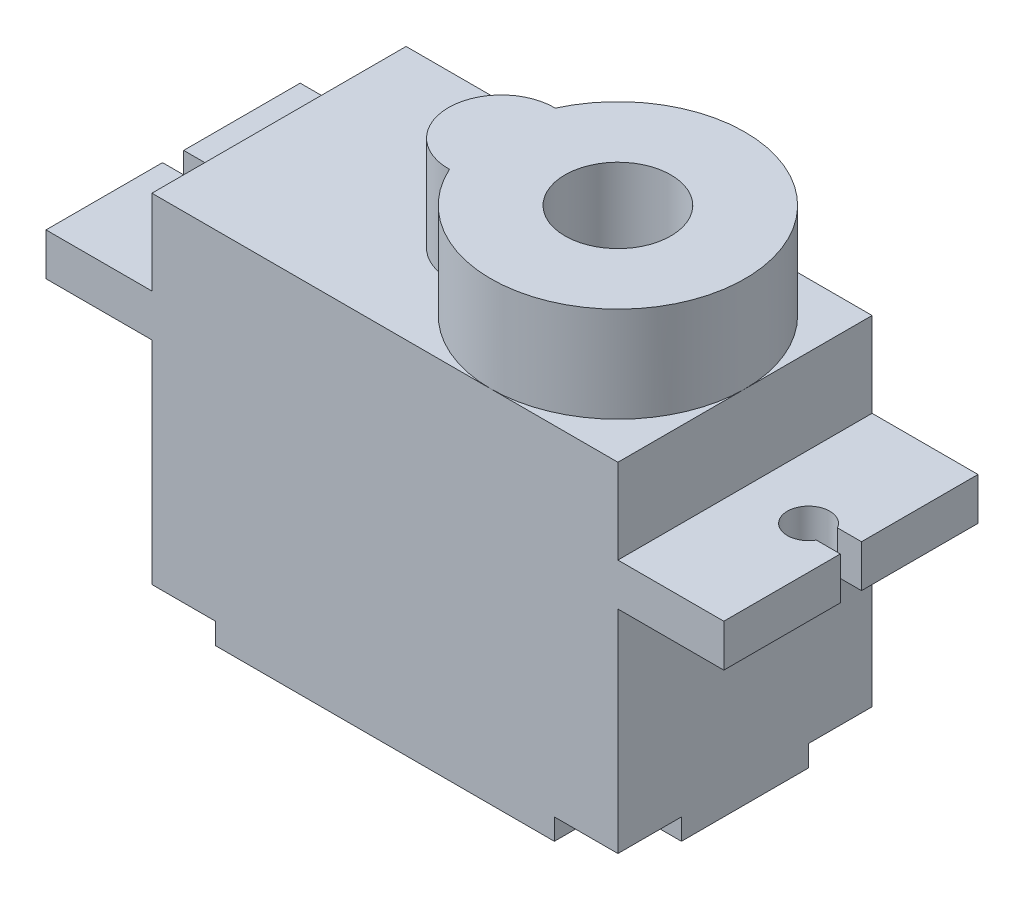
SolidWorks part; units mm, degrees
material "Plástico personalizado"
ref_plane "Alzado" through (0, 0, 0) normal (0, 0, 1) x (1, 0, 0)
ref_plane "Planta" through (0, 0, 0) normal (0, 1, 0) x (1, 0, 0)
ref_plane "Vista lateral" through (0, 0, 0) normal (1, 0, 0) x (0, 0, -1)
sketch "Croquis1" plane through (0, 0, 0) normal (0, 1, 0) x (1, 0, 0)
  line L1 (11, -6) -> (-11, -6)
  line L2 (11, -6) -> (11, 6)
  line L3 (11, 6) -> (-11, 6)
  line L4 (-11, -6) -> (-11, 6)
  line L5 (11, -6) -> (-11, 6) construction
  line L6 (11, 6) -> (-11, -6) construction
  point P0 (0, 0)
  dimension "D1" = 22
  dimension "D2" = 12
extrude "Saliente-Extruir1" add sketch "Croquis1" along normal blind 11
sketch "Croquis3" plane through (0, 11, 0) normal (0, 1, 0) x (1, 0, 0)
  line L0 (-11, 6) -> (-11, -6) construction
  line L1 (-6, 6) -> (-16, 6)
  line L2 (-6, 6) -> (-6, -6)
  line L3 (-6, -6) -> (-16, -6)
  line L4 (-16, 6) -> (-16, -6)
  line L5 (-6, 6) -> (-16, -6) construction
  line L6 (-6, -6) -> (-16, 6) construction
  line L7 (11, -6) -> (11, 6) construction
  line L8 (6, -6) -> (16, -6)
  line L9 (6, -6) -> (6, 6)
  line L10 (6, 6) -> (16, 6)
  line L11 (16, -6) -> (16, 6)
  line L12 (6, -6) -> (16, 6) construction
  line L13 (6, 6) -> (16, -6) construction
  point P0 (-11, 0)
  point P7 (11, 0)
  dimension "D1" = 10
  dimension "D2" = 10
extrude "Saliente-Extruir2" add sketch "Croquis3" along normal blind 2
sketch "Croquis4" plane through (0, 11, 0) normal (0, 1, 0) x (1, 0, 0)
  line L1 (6, -6) -> (-6, -6)
  line L2 (6, -6) -> (6, 6)
  line L3 (6, 6) -> (-6, 6)
  line L4 (-6, -6) -> (-6, 6)
  line L5 (6, -6) -> (-6, 6) construction
  line L6 (6, 6) -> (-6, -6) construction
  point P0 (0, 0)
extrude "Saliente-Extruir3" add sketch "Croquis4" along normal blind 6
sketch "Croquis5" plane through (0, 13, 0) normal (0, 1, 0) x (1, 0, 0)
  line L0 (-16, 0) -> (-16, 0.5)
  line L1 (-16, 6) -> (-16, -6) construction
  line L2 (-16, 0) -> (-16, -0.5)
  line L3 (-16, 0) -> (-15, 0)
  line L4 (-16, 0.5) -> (-15, 0.5)
  line L5 (-16, -0.5) -> (-15.9117, -0.5)
  line L7 (-15.9117, -0.5) -> (-15, -0.5)
  line L9 (-15, 0.5) -> (-14.866, 0.5)
  line L10 (-15, -0.5) -> (-14.866, -0.5)
  arc A0 (-14.866, -0.5) -> (-14.866, 0.5) centre (-14, 0) ccw
  dimension "D1" = 0.5
  dimension "D2" = 0.5
  dimension "D3" = 1
  dimension "D4" = 1
extrude "Cortar-Extruir1" cut sketch "Croquis5" against normal blind 2
sketch "Croquis6" plane through (0, 13, 0) normal (0, 1, 0) x (1, 0, 0)
  line L0 (6, -6) -> (16, -6) construction
  line L1 (-6, 6) -> (-11, 6)
  line L2 (-6, 6) -> (-6, -6)
  line L3 (-6, -6) -> (-11, -6)
  line L4 (-11, 6) -> (-11, -6)
  line L5 (6, 6) -> (11, 6)
  line L6 (6, 6) -> (6, -6)
  line L7 (6, -6) -> (11, -6)
  line L8 (11, 6) -> (11, -6)
extrude "Saliente-Extruir4" add sketch "Croquis6" along normal blind 4
sketch "Croquis7" plane through (0, 13, 0) normal (0, 1, 0) x (1, 0, 0)
  line L1 (16, -6) -> (16, 6) construction
  line L2 (16, 0) -> (16, 0.5)
  line L3 (16, 0) -> (16, -0.5)
  line L5 (16, 0.5) -> (14.907, 0.5)
  line L6 (16, -0.5) -> (15, -0.5)
  line L7 (15, -0.5) -> (14.866, -0.5)
  line L8 (14.907, 0.5) -> (14.866, 0.5)
  arc A0 (14.866, 0.5) -> (14.866, -0.5) centre (14, 0) ccw
  dimension "D2" = 0.5
  dimension "D3" = 0.5
extrude "Cortar-Extruir2" cut sketch "Croquis7" against normal blind 4
sketch "Croquis8" plane through (0, 17, 0) normal (0, 1, 0) x (1, 0, 0)
  circle A0 centre (5, 0) radius 6
extrude "Saliente-Extruir5" add sketch "Croquis8" along normal blind 4.5
sketch "Croquis9" plane through (0, 17, 0) normal (0, 1, 0) x (1, 0, 0)
  line L0 (11, 0) -> (-0.5, 0)
  line L1 (11, -6) -> (11, 6) construction
  circle A0 centre (-0.5, 0) radius 2.5
  arc M2 (5, -6) -> (5, 6) centre (5, 0) cw
  dimension "D2" = 5
  dimension "D1" = 11.5
extrude "Saliente-Extruir6" add sketch "Croquis9" along normal up to surface (4.5 mm away) contours A0 M2 up to face at (5, 21.5, 6)
sketch "Croquis10" plane through (0, 0, 0) normal (0, -1, 0) x (-1, 0, 0)
  line L0 (11, -6) -> (11, -3)
  line L1 (11, -6) -> (-11, -6) construction
  line L2 (11, 6) -> (11, -6) construction
  line L3 (11, -6) -> (8, -6)
  line L4 (8, -6) -> (8, -3)
  line L5 (8, -3) -> (11, -3)
  dimension "D1" = 3
  dimension "D2" = 3
extrude "Cortar-Extruir3" cut sketch "Croquis10" against normal blind 1
fillet "Redondeo1" radius 1.5 1 edges at (-8, 0.5, 3)
sketch "Croquis11" plane through (0, 0, 0) normal (0, -1, 0) x (-1, 0, 0)
  line L0 (11, 6) -> (8, 6)
  line L1 (-11, 6) -> (11, 6) construction
  line L2 (11, 6) -> (11, 3)
  line L3 (11, 6) -> (11, -3) construction
  line L4 (8, 6) -> (8, 3)
  line L5 (8, 3) -> (11, 3)
  line L6 (-11, -6) -> (-8, -6)
  line L7 (8, -6) -> (-11, -6) construction
  line L8 (-11, -6) -> (-11, -3)
  line L9 (-11, -6) -> (-11, 6) construction
  line L10 (-11, 6) -> (-8, 6)
  line L11 (-11, 6) -> (-11, 3)
  line L12 (-11, -3) -> (-8, -3)
  line L13 (-8, -3) -> (-8, -6)
  line L14 (-8, 6) -> (-8, 3)
  line L15 (-8, 3) -> (-11, 3)
  dimension "D1" = 3
  dimension "D2" = 3
  dimension "D3" = 3
  dimension "D4" = 3
  dimension "D5" = 3
  dimension "D6" = 3
extrude "Cortar-Extruir4" cut sketch "Croquis11" against normal blind 1
fillet "Redondeo3" radius 1.5 3 edges at (8, 0.5, 3) (8, 0.5, -3) (-8, 0.5, -3)
sketch "Croquis12" plane through (0, 1, 0) normal (0, -1, 0) x (-1, 0, 0)
  line L0 (8, -6) -> (11, -6) construction
  line L1 (11, -6) -> (11, -3) construction
  line L2 (11, 6) -> (8, 6) construction
  line L4 (-11, -3) -> (-11, -6) construction
  circle A0 centre (9.75, -4.75) radius 1
  circle A1 centre (9.75, 4.75) radius 1
  circle A2 centre (-9.75, -4.75) radius 1
  circle A3 centre (-9.75, 4.75) radius 1
  dimension "D5" = 2
  dimension "D6" = 2
  dimension "D7" = 2
  dimension "D8" = 2
  dimension "D1" = 1.25
  dimension "D2" = 1.25
  dimension "D3" = 1.25
  dimension "D4" = 1.25
extrude "Cortar-Extruir5" cut sketch "Croquis12" against normal blind 3
sketch "Croquis13" plane through (0, 21.5, 0) normal (0, 1, 0) x (1, 0, 0)
  circle A0 centre (5, 0) radius 2.5
  dimension "D1" = 5
extrude "Cortar-Extruir6" cut sketch "Croquis13" against normal blind 5
